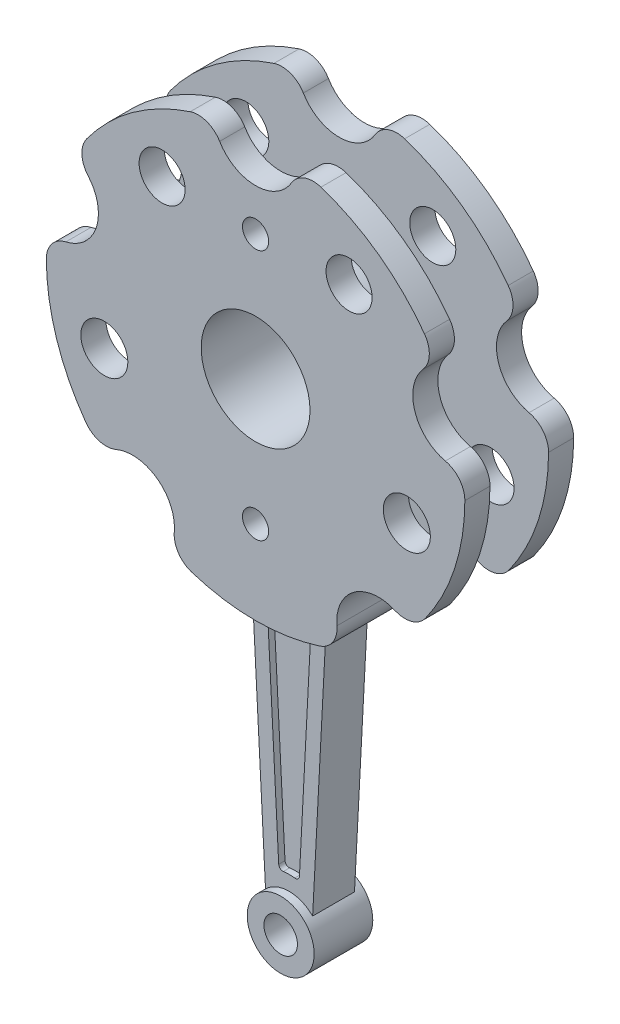
SolidWorks part; units mm, degrees
material "4032-T6"
ref_plane "Front Plane" through (0, 0, 0) normal (0, 0, 1) x (1, 0, 0)
ref_plane "Top Plane" through (0, 0, 0) normal (0, 1, 0) x (1, 0, 0)
ref_plane "Right Plane" through (0, 0, 0) normal (1, 0, 0) x (0, 0, -1)
sketch "Sketch1" plane through (0, 0, 0) normal (0, 0, 1) x (1, 0, 0)
  line L0 (-8.94, -49.1943) -> (-5.63, -112.6428)
  line L1 (0, 73.8968) -> (0, -205.7441) construction
  line L2 (0, 0) -> (-41.2808, 56.8182) construction
  line L3 (0, 0) -> (-73.773, -23.9703) construction
  line L4 (8.94, -49.1943) -> (5.63, -112.6428)
  line L5 (-5.164, -54.3927) -> (-2.4786, -105.8702)
  line L6 (5.164, -54.3927) -> (2.4786, -105.8702)
  arc A0 (-15.6125, 47.5) -> (-40.3507, 29.5267) centre (0, 0) ccw
  circle A1 centre (0, 0) radius 38 construction
  circle A2 centre (0, 0) radius 30 construction
  circle A3 centre (-22.3358, 30.7426) radius 5.5
  circle A4 centre (22.3358, 30.7426) radius 5.5
  circle A5 centre (-36.1401, -11.7426) radius 5.6168
  circle A6 centre (36.1401, -11.7426) radius 5.6168
  arc A7 (-8.5869, 44.875) -> (8.5869, 44.875) centre (0, 50) ccw
  arc A8 (40.0252, 22.0337) -> (45.3322, 5.7005) centre (47.5528, 15.4508) ccw
  arc A9 (33.3238, -31.2574) -> (19.4299, -41.3519) centre (29.3893, -40.4508) ccw
  arc A10 (-19.4299, -41.3519) -> (-33.3238, -31.2574) centre (-29.3893, -40.4508) ccw
  arc A11 (-45.3322, 5.7005) -> (-40.0252, 22.0337) centre (-47.5528, 15.4508) ccw
  arc A12 (40.3507, 29.5267) -> (15.6125, 47.5) centre (0, 0) ccw
  arc A13 (-49.9997, -0.1701) -> (-40.5506, -29.2515) centre (0, 0) ccw
  arc A14 (-15.289, -47.6051) -> (15.289, -47.6051) centre (0, 0) ccw
  arc A15 (40.5506, -29.2515) -> (49.9997, -0.1701) centre (0, 0) ccw
  arc A16 (-40.3507, 29.5267) -> (-40.0252, 22.0337) centre (-35.5086, 25.9835) ccw
  arc A17 (-8.5869, 44.875) -> (-15.6125, 47.5) centre (-13.739, 41.8) ccw
  arc A18 (8.5869, 44.875) -> (15.6125, 47.5) centre (13.739, 41.8) cw
  arc A19 (40.0252, 22.0337) -> (40.3507, 29.5267) centre (35.5086, 25.9835) ccw
  arc A20 (40.5506, -29.2515) -> (33.3238, -31.2574) centre (35.6845, -25.7413) cw
  arc A21 (15.289, -47.6051) -> (19.4299, -41.3519) centre (13.4543, -41.8925) ccw
  arc A22 (-19.4299, -41.3519) -> (-15.289, -47.6051) centre (-13.4543, -41.8925) ccw
  arc A23 (-49.9997, -0.1701) -> (-45.3322, 5.7005) centre (-43.9997, -0.1497) cw
  arc A24 (-33.3238, -31.2574) -> (-40.5506, -29.2515) centre (-35.6845, -25.7413) cw
  arc A25 (45.3322, 5.7005) -> (49.9997, -0.1701) centre (43.9997, -0.1497) cw
  circle A26 centre (0, -118) radius 4
  circle A27 centre (0, -118) radius 7.7715
  arc A28 (-4.089, -53.3435) -> (4.089, -53.3435) centre (0, 0) ccw
  arc A29 (-1.3593, -106.8108) -> (1.3593, -106.8108) centre (0, -118) cw
  arc A30 (2.4786, -105.8702) -> (1.3593, -106.8108) centre (1.4799, -105.8181) cw
  arc A31 (-2.4786, -105.8702) -> (-1.3593, -106.8108) centre (-1.4799, -105.8181) ccw
  arc A32 (5.164, -54.3927) -> (4.089, -53.3435) centre (4.1654, -54.3406) ccw
  arc A33 (-5.164, -54.3927) -> (-4.089, -53.3435) centre (-4.1654, -54.3406) cw
  circle A35 centre (0, 30) radius 3.125
  circle A36 centre (0, -30) radius 3.125
  circle A37 centre (0, 0) radius 13
  point P31 (0, 0.0629)
  point P42 (43.5271, 24.6047)
  point P49 (-20.7519, -45.4902)
  point P68 (2.4201, -106.9914)
  point P71 (-2.4201, -106.9914)
  point P74 (5.224, -53.2443)
  point P77 (-5.224, -53.2443)
  dimension "D1" = 60
  dimension "D2" = 76
  dimension "D3" = 100
  dimension "D4" = 5.63
  dimension "D7" = 3.5
  dimension "D9" = 6
  dimension "D10" = 3.5
  dimension "D11" = 3.5
  dimension "D12" = 1
  dimension "D13" = 1
  dimension "D14" = 1
  dimension "D15" = 1
  dimension "D16" = 6
  dimension "D17" = 6.25
  dimension "D18" = 6.25
  dimension "D19" = 26
  dimension "D5" = 36
  dimension "D6" = 8.94
  dimension "D8" = 118
extrude "Boss-Extrude2" add sketch "Sketch1" along normal mid plane 26 contours A25 A8 A19 A12 A18 A7 A17 A0 A16 A11 A23 A13 A24 A10 A22 A14 A21 A9 A20 A15 A37 A36 A35 A4 A3 A5 A6
sketch "Sketch3" plane through (0, 0, 0) normal (0, 0, 1) x (1, 0, 0)
  line L0 (-12.9313, -17.7984) -> (-23.5114, -32.3607)
  line L1 (12.9313, -17.7984) -> (23.5114, -32.3607)
  arc A0 (12.9313, -17.7984) -> (-12.9313, -17.7984) centre (0, 0) ccw
  arc A1 (-19.4299, -41.3519) -> (-33.3238, -31.2574) centre (-29.3893, -40.4508) ccw construction
  arc A2 (33.3238, -31.2574) -> (19.4299, -41.3519) centre (29.3893, -40.4508) ccw construction
  arc A3 (-19.4299, -41.3519) -> (-23.5114, -32.3607) centre (-29.3893, -40.4508) ccw
  arc A4 (23.5114, -32.3607) -> (19.4299, -41.3519) centre (29.3893, -40.4508) ccw
  arc A5 (-19.4299, -41.3519) -> (-15.289, -47.6051) centre (-13.4543, -41.8925) ccw
  arc A6 (15.289, -47.6051) -> (19.4299, -41.3519) centre (13.4543, -41.8925) ccw
  arc A7 (-15.289, -47.6051) -> (15.289, -47.6051) centre (0, 0) ccw
  dimension "D1" = 44
extrude "Cut-Extrude2" cut sketch "Sketch3" against normal mid plane 14 flip side to cut
sketch "Sketch4" plane through (0, 0, 0) normal (0, 0, 1) x (1, 0, 0)
  line L0 (0, 98.3613) -> (0, -171.764) construction
  line L1 (-5.63, -112.3164) -> (-8.94, -49.1943)
  line L2 (5.63, -112.3164) -> (8.94, -49.1943)
  line L3 (-5.1871, -53.9255) -> (-2.4753, -105.6399)
  line L4 (5.1871, -53.9255) -> (2.4753, -105.6399)
  circle A0 centre (0, -118) radius 8
  circle A1 centre (0, -118) radius 4
  arc A2 (-15.289, -47.6051) -> (15.289, -47.6051) centre (0, 0) ccw construction
  arc A3 (-4.111, -52.8761) -> (4.111, -52.8761) centre (0, 0) ccw
  arc A4 (-1.3585, -106.5805) -> (1.3585, -106.5805) centre (0, -118) cw
  arc A5 (-2.4753, -105.6399) -> (-1.3585, -106.5805) centre (-1.4767, -105.5875) ccw
  arc A6 (2.4753, -105.6399) -> (1.3585, -106.5805) centre (1.4767, -105.5875) cw
  arc A7 (5.1871, -53.9255) -> (4.111, -52.8761) centre (4.1885, -53.8731) ccw
  arc A8 (-5.1871, -53.9255) -> (-4.111, -52.8761) centre (-4.1885, -53.8731) cw
  dimension "D1" = 8
  dimension "D2" = 16
  dimension "D8" = 3.5
  dimension "D9" = 1
  dimension "D10" = 1
  dimension "D11" = 1
  dimension "D12" = 1
  dimension "D3" = 118
  dimension "D4" = 8.94
  dimension "D5" = 5.63
  dimension "D6" = 3.5
  dimension "D7" = 3.5
extrude "Boss-Extrude3" add sketch "Sketch4" along normal mid plane 7 separate body contours A3 L0 A4 A6 L4 A7 | L0 A3 A8 L3 A5 A4
sketch "Sketch5" plane through (0, 0, 0) normal (0, 0, 1) x (1, 0, 0)
  line L0 (0, -14.3) -> (0, 14.3) construction
  line L1 (-8.94, -49.1943) -> (-5.63, -112.3164)
  line L2 (8.94, -49.1943) -> (5.63, -112.3164)
  line L3 (-5.1871, -53.9255) -> (-2.4753, -105.6399)
  line L4 (2.4753, -105.6399) -> (5.1871, -53.9255)
  line L5 (-5.1871, -53.9255) -> (-2.4753, -105.6399)
  line L6 (2.4753, -105.6399) -> (5.1871, -53.9255)
  line L7 (0, 182.7366) -> (0, -316.1183) construction
  circle A0 centre (0, -118) radius 8
  circle A1 centre (0, -118) radius 4
  arc A2 (-15.289, -47.6051) -> (15.289, -47.6051) centre (0, 0) ccw construction
  arc A3 (-8.94, -49.1943) -> (8.94, -49.1943) centre (0, 0) ccw
  arc A8 (-4.111, -52.8761) -> (4.111, -52.8761) centre (0, 0) ccw
  arc A9 (-4.111, -52.8761) -> (-5.1871, -53.9255) centre (-4.1885, -53.8731) ccw
  arc A10 (-2.4753, -105.6399) -> (-1.3585, -106.5805) centre (-1.4767, -105.5875) ccw
  arc A11 (1.3585, -106.5805) -> (-1.3585, -106.5805) centre (0, -118) ccw
  arc A12 (1.3585, -106.5805) -> (2.4753, -105.6399) centre (1.4767, -105.5875) ccw
  arc A13 (5.1871, -53.9255) -> (4.111, -52.8761) centre (4.1885, -53.8731) ccw
  arc A14 (-4.111, -52.8761) -> (4.111, -52.8761) centre (0, 0) ccw
  arc A15 (-4.111, -52.8761) -> (-5.1871, -53.9255) centre (-4.1885, -53.8731) ccw
  arc A16 (-2.4753, -105.6399) -> (-1.3585, -106.5805) centre (-1.4767, -105.5875) ccw
  arc A17 (1.3585, -106.5805) -> (-1.3585, -106.5805) centre (0, -118) ccw
  arc A18 (1.3585, -106.5805) -> (2.4753, -105.6399) centre (1.4767, -105.5875) ccw
  arc A19 (5.1871, -53.9255) -> (4.111, -52.8761) centre (4.1885, -53.8731) ccw
  dimension "D1" = 16
  dimension "D2" = 8
  dimension "D3" = 118
  dimension "D5" = 8.94
  dimension "D6" = 5.63
  dimension "D4" = 0
extrude "Boss-Extrude4" add sketch "Sketch5" along normal mid plane 10 contours A3 L7 A14 A19 L6 A18 A17 A0 L2 | L7 A3 L1 A0 A17 A16 L5 A15 A14
sketch "Sketch6" plane through (0, 0, 0) normal (0, 0, 1) x (1, 0, 0)
  line L0 (0, -14.3) -> (0, 14.3) construction
  line L3 (-8.94, -49.1943) -> (-5.63, -112.3164)
  line L4 (5.63, -112.3164) -> (8.94, -49.1943)
  line L5 (-8.94, -49.1943) -> (-5.63, -112.3164)
  line L6 (5.63, -112.3164) -> (8.94, -49.1943)
  circle A0 centre (0, -118) radius 8
  circle A1 centre (0, -118) radius 4
  arc A5 (-8.94, -49.1943) -> (8.94, -49.1943) centre (0, 0) ccw
  arc A6 (5.63, -112.3164) -> (-5.63, -112.3164) centre (0, -118) ccw
  arc A7 (-8.94, -49.1943) -> (8.94, -49.1943) centre (0, 0) ccw
  arc A8 (5.63, -112.3164) -> (-5.63, -112.3164) centre (0, -118) ccw
  dimension "D3" = 0
extrude "Boss-Extrude5" add sketch "Sketch6" along normal mid plane 14 contours A0 A1
